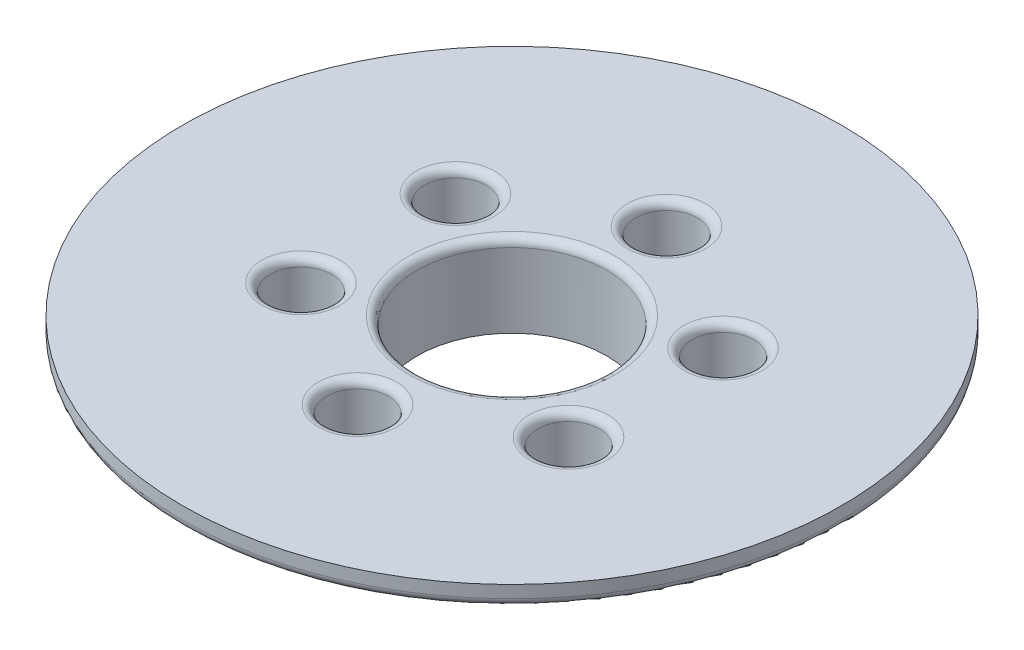
SolidWorks part; units mm, degrees
ref_plane "Front" through (0, 0, 0) normal (0, 0, 1) x (1, 0, 0)
ref_plane "Top" through (0, 0, 0) normal (0, 1, 0) x (1, 0, 0)
ref_plane "Right" through (0, 0, 0) normal (1, 0, 0) x (0, 0, -1)
sketch "Sketch1" plane through (0, 0, 0) normal (0, 1, 0) x (1, 0, 0)
  circle A0 centre (0, 0) radius 29.21
  circle A1 centre (0, 0) radius 31.75
  dimension "D1" = 58.42
  dimension "D2" = 63.5
extrude "Boss-Extrude1" add sketch "Sketch1" along normal blind 3.175
sketch "Sketch2" plane through (0, 3.175, 0) normal (0, 1, 0) x (1, 0, 0)
  circle A0 centre (0, 0) radius 31.75 construction
  circle A1 centre (0, 0) radius 31.75
extrude "Boss-Extrude2" add sketch "Sketch2" along normal blind 9.525
sketch "Sketch3" plane through (0, 3.175, 0) normal (0, -1, 0) x (1, 0, 0)
  circle A0 centre (0, 0) radius 14.605
  dimension "D1" = 29.21
extrude "Cut-Extrude1" cut sketch "Sketch3" against normal through all
sketch "Sketch4" plane through (0, 12.7, 0) normal (0, 1, 0) x (1, 0, 0)
  circle A0 centre (0, 0) radius 14.605 construction
  circle A1 centre (0, 0) radius 14.605
  circle A2 centre (0, 0) radius 50.8
  circle A3 centre (0, 0) radius 31.75 construction
  dimension "D1" = 19.05
extrude "Rim" add sketch "Sketch4" along normal blind 3.175
sketch "Sketch5" plane through (0, 3.175, 0) normal (0, -1, 0) x (1, 0, 0)
  line L0 (0, 0) -> (0, 23.8125) construction
  circle A0 centre (0, 23.8125) radius 2.667
  circle A1 centre (20.6222, 11.9063) radius 2.667
  circle A2 centre (20.6222, -11.9062) radius 2.667
  circle A3 centre (0, -23.8125) radius 2.667
  circle A4 centre (-20.6222, -11.9063) radius 2.667
  circle A5 centre (-20.6222, 11.9062) radius 2.667
  point P17 (0, 0)
  dimension "D2" = 5.334
  dimension "D1" = 23.8125
  dimension "D3" = 6
extrude "r" cut sketch "Sketch5" against normal through all
sketch "Sketch6" plane through (0, 15.875, 0) normal (0, 1, 0) x (1, 0, 0)
  circle A0 centre (20.6222, -11.9063) radius 4.7625
  circle A1 centre (0, -23.8125) radius 4.7625
  circle A2 centre (-20.6222, -11.9062) radius 4.7625
  circle A3 centre (-20.6222, 11.9063) radius 4.7625
  circle A4 centre (0, 23.8125) radius 4.7625
  circle A5 centre (20.6222, 11.9062) radius 4.7625
  point P15 (0, 0)
  dimension "D1" = 9.525
  dimension "D2" = 6
extrude "Cut-Extrude3" cut sketch "Sketch6" against normal blind 8.255
fillet "Fillet1" radius 1.27 8 edges at (0, 15.875, 14.605) (0, 15.875, 28.575) (-20.6222, 15.875, 16.6687) (-20.6222, 15.875, -7.1438) (0, 15.875, -19.05) (20.6222, 15.875, 16.6688) (20.6222, 15.875, -7.1437) (0, 12.7, 50.8)
